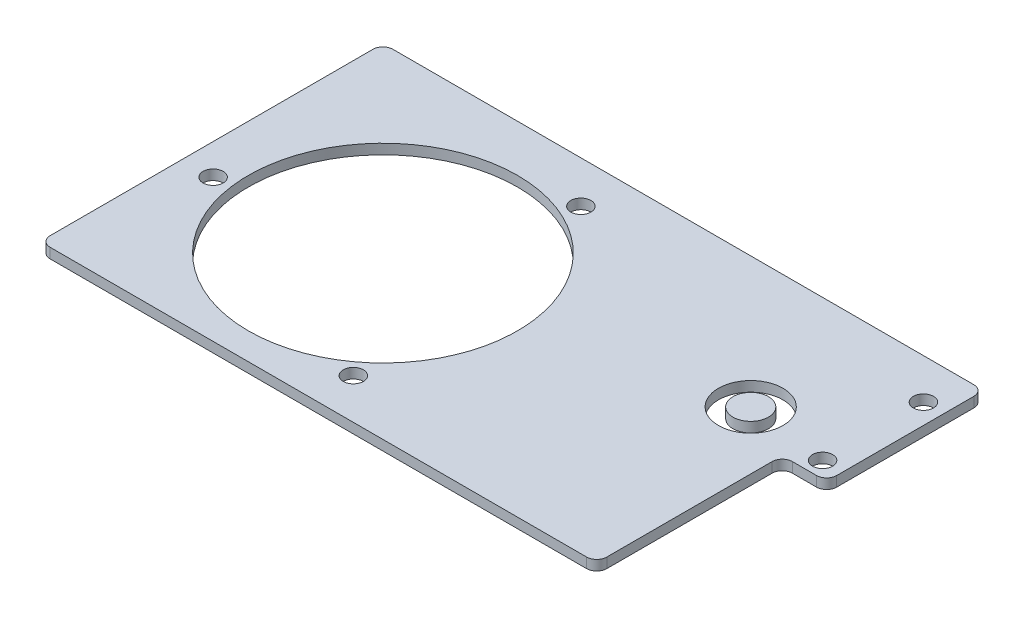
SolidWorks part; units mm, degrees
ref_plane "Front Plane" through (0, 0, 0) normal (0, 0, 1) x (1, 0, 0)
ref_plane "Top Plane" through (0, 0, 0) normal (0, 1, 0) x (1, 0, 0)
ref_plane "Right Plane" through (0, 0, 0) normal (1, 0, 0) x (0, 0, -1)
sketch "Sketch1" plane through (0, 0, 0) normal (0, 1, 0) x (1, 0, 0)
  line L0 (0, 114.3) -> (0, -101.6) construction
  line L1 (257.81, 114.3) -> (-107.95, 114.3)
  line L2 (264.16, 107.95) -> (264.16, 21.59)
  line L3 (229.87, -101.6) -> (-107.95, -101.6)
  line L4 (-114.3, 107.95) -> (-114.3, -95.25)
  line L5 (242.57, 15.24) -> (257.81, 15.24)
  line L6 (251.46, 0) -> (251.46, 114.3) construction
  line L7 (-114.3, 0) -> (285.75, 0) construction
  line L8 (0, 0) -> (-114.3, -39.3566) construction
  line L11 (236.22, -95.25) -> (236.22, 8.89)
  circle A0 centre (0, 0) radius 84.7725
  circle A1 centre (0, 0) radius 95.25 construction
  circle A2 centre (-94.8682, -12.0662) radius 6.35
  arc A3 (236.22, 8.89) -> (242.57, 15.24) centre (242.57, 8.89) cw
  arc A4 (-107.95, 114.3) -> (-114.3, 107.95) centre (-107.95, 107.95) ccw
  circle A5 centre (36.7916, 87.8575) radius 6.35
  circle A6 centre (57.4982, -76.1251) radius 6.35
  arc A7 (-107.95, -101.6) -> (-114.3, -95.25) centre (-107.95, -95.25) cw
  arc A8 (229.87, -101.6) -> (236.22, -95.25) centre (229.87, -95.25) ccw
  arc A9 (257.81, 15.24) -> (264.16, 21.59) centre (257.81, 21.59) ccw
  arc A10 (257.81, 114.3) -> (264.16, 107.95) centre (257.81, 107.95) cw
  circle A11 centre (251.46, 88.9) radius 6.35
  circle A12 centre (251.46, 25.4) radius 6.35
  circle A13 centre (-94.8682, -12.0662) radius 6.35 construction
  point P0 (0, 0)
  point P11 (0, 0)
  point P21 (236.22, -6.35)
  point P32 (236.22, -101.6)
  point P46 (-0.1928, -0.1113)
  dimension "D3" = 169.545
  dimension "D5" = 190.5
  dimension "D6" = 12.7
  dimension "D7" = 114.3
  dimension "D8" = 264.16
  dimension "D11" = 6.35
  dimension "D12" = 86.36
  dimension "D14" = 12.7
  dimension "D1" = 114.3
  dimension "D2" = 101.6
  dimension "D4" = 19
  dimension "D9" = 95.25
  dimension "D10" = 27.94
  dimension "D13" = 12.7
  dimension "D15" = 25.4
  dimension "D16" = 3
extrude "Boss-Extrude1" add sketch "Sketch1" along normal blind 6.35
sketch "Sketch2" plane through (0, 0, 0) normal (0, -1, 0) x (1, 0, 0)
  line L0 (-114.3, -107.95) -> (-114.3, 95.25) construction
  line L1 (257.81, -114.3) -> (-107.95, -114.3) construction
  line L2 (264.16, -21.59) -> (264.16, -107.95) construction
  line L3 (-107.95, 101.6) -> (229.87, 101.6) construction
  line L4 (-114.3, -107.95) -> (-114.3, 95.25)
  line L5 (257.81, -114.3) -> (-107.95, -114.3)
  line L6 (264.16, -21.59) -> (264.16, -107.95)
  line L7 (-107.95, 101.6) -> (229.87, 101.6)
  line L8 (74.93, -114.3) -> (74.93, 101.6) construction
  line L9 (-114.3, -6.35) -> (264.16, -6.35) construction
  line L11 (319.405, 146.05) -> (-169.545, 146.05)
  line L12 (319.405, 146.05) -> (319.405, -158.75)
  line L13 (319.405, -158.75) -> (-169.545, -158.75)
  line L14 (-169.545, 146.05) -> (-169.545, -158.75)
  line L15 (319.405, 146.05) -> (-169.545, -158.75) construction
  line L16 (319.405, -158.75) -> (-169.545, 146.05) construction
  point P12 (74.93, -6.35)
  dimension "D1" = 378.46
  dimension "D2" = 215.9
  dimension "D3" = 488.95
  dimension "D4" = 304.8
sketch "Sketch3" plane through (0, 6.35, 0) normal (0, 1, 0) x (1, 0, 0)
  circle A0 centre (0, 0) radius 84.7725 construction
  point P0 (84.7725, 0)
sketch "Sketch4" plane through (0, 6.35, 0) normal (0, 1, 0) x (1, 0, 0)
  circle A1 centre (199.6633, 31.9496) radius 29.4567 construction
  circle A2 centre (199.6633, 31.9496) radius 20.32
  circle A3 centre (199.6633, 31.9496) radius 11.176 construction
  circle A4 centre (199.6633, 31.9496) radius 11.176
  dimension "D1" = 40.64
extrude "Cut-Extrude1" cut sketch "Sketch4" against normal blind 9.652
